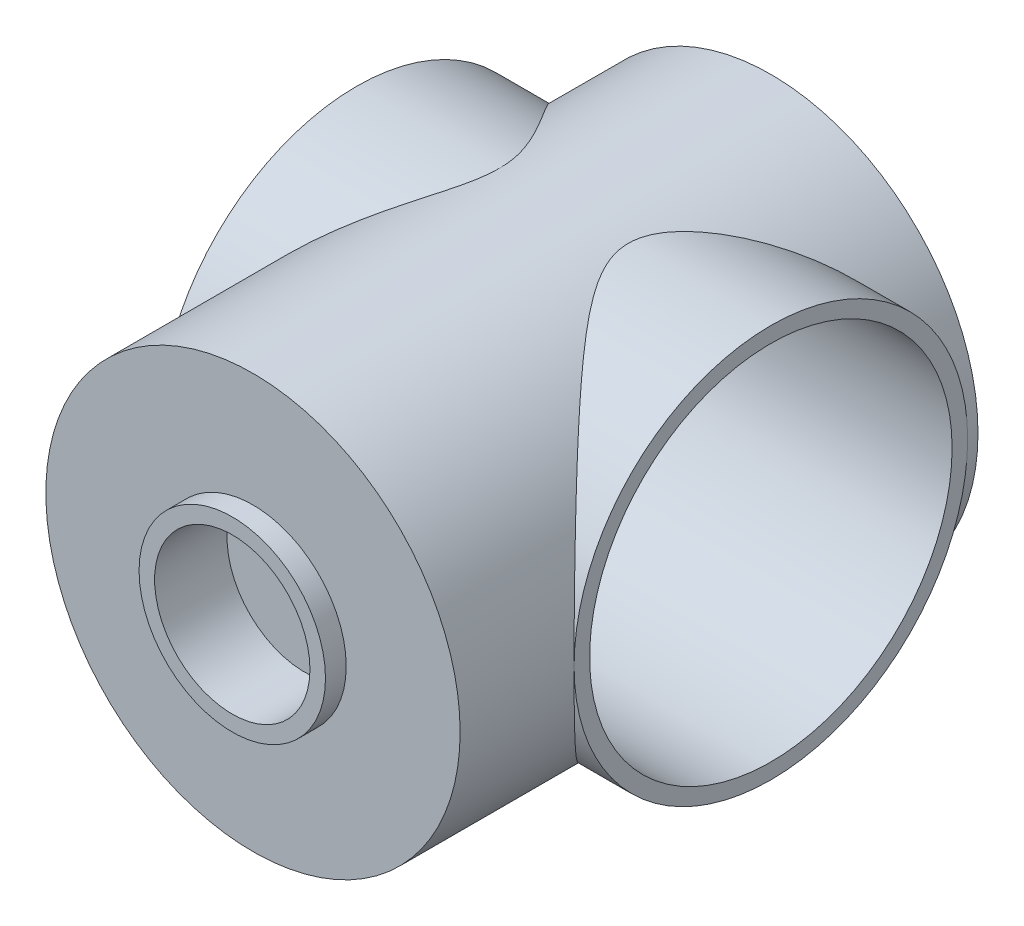
SolidWorks part; units mm, degrees
ref_plane "Front Plane" through (0, 0, 0) normal (0, 0, 1) x (1, 0, 0)
ref_plane "Top Plane" through (0, 0, 0) normal (0, 1, 0) x (1, 0, 0)
ref_plane "Right Plane" through (0, 0, 0) normal (1, 0, 0) x (0, 0, -1)
sketch "Sketch1" plane through (0, 0, 0) normal (0, 0, 1) x (1, 0, 0)
  circle A0 centre (0, 0) radius 20
  dimension "D1" = 40
extrude "Boss-Extrude1" add sketch "Sketch1" along normal blind 50
sketch "Sketch2" plane through (0, 0, 0) normal (1, 0, 0) x (0, 0, -1)
  circle A0 centre (-20, 0) radius 19
  dimension "D1" = 38
  dimension "D2" = 20
extrude "Boss-Extrude2" add sketch "Sketch2" along normal mid plane 40
sketch "Sketch4" plane through (20, 0, 0) normal (1, 0, 0) x (0, 0, -1)
  circle A0 centre (-20, 0) radius 17.5
  dimension "D1" = 35
extrude "Cut-Extrude1" cut sketch "Sketch4" against normal blind 40
sketch "Sketch5" plane through (0, 0, 50) normal (0, 0, 1) x (1, 0, 0)
  circle A0 centre (0, 0) radius 7.5
  dimension "D1" = 15
extrude "Cut-Extrude2" cut sketch "Sketch5" against normal blind 5
sketch "Sketch6" plane through (0, 0, 50) normal (0, 0, 1) x (1, 0, 0)
  circle A0 centre (0, 0) radius 7.5
  circle A1 centre (0, 0) radius 9
  dimension "D1" = 18
extrude "Boss-Extrude3" add sketch "Sketch6" along normal blind 2
